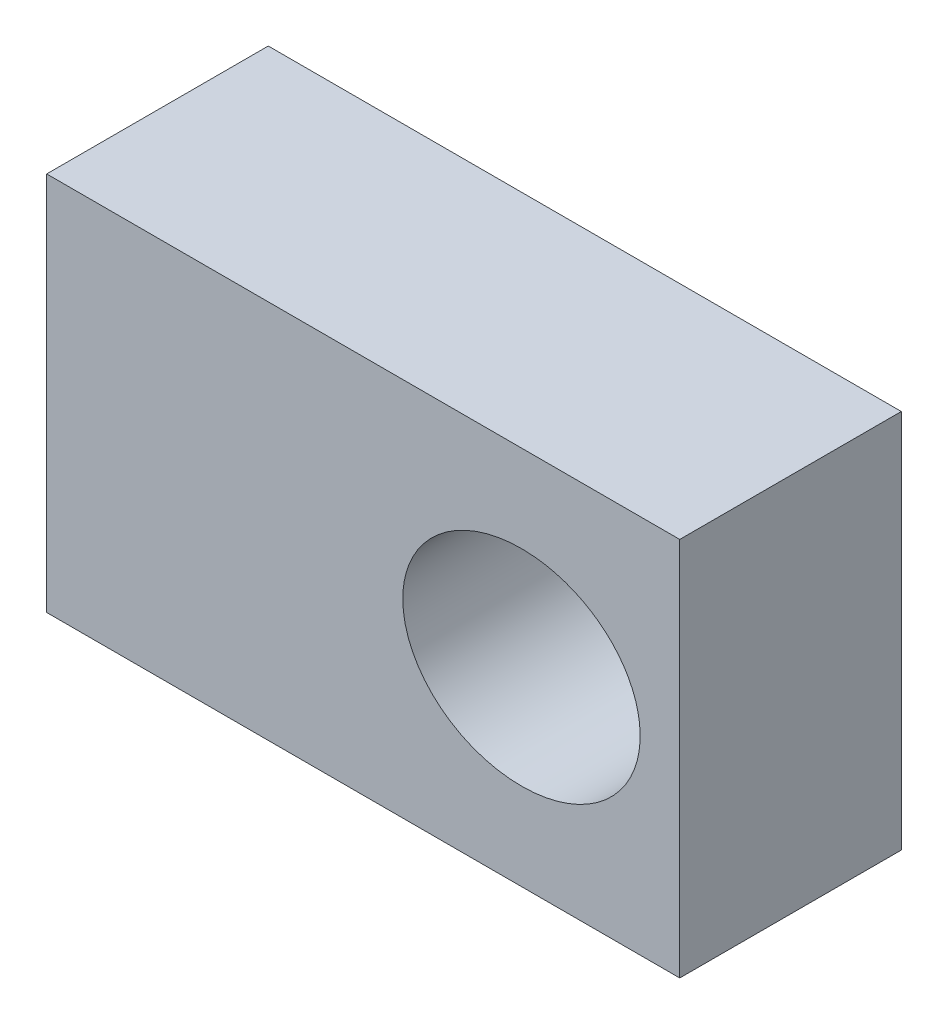
SolidWorks part; units mm, degrees
ref_plane "Front Plane" through (0, 0, 0) normal (0, 0, 1) x (1, 0, 0)
ref_plane "Top Plane" through (0, 0, 0) normal (0, 1, 0) x (1, 0, 0)
ref_plane "Right Plane" through (0, 0, 0) normal (1, 0, 0) x (0, 0, -1)
sketch "Sketch1" plane through (0, 0, 0) normal (0, 0, 1) x (1, 0, 0)
  line L0 (-37.5, 0) -> (37.5, 0) construction
  line L1 (-150, 60) -> (50, 60)
  line L2 (-150, 60) -> (-150, -60)
  line L3 (-150, -60) -> (50, -60)
  line L4 (50, 60) -> (50, -60)
  line L5 (0, 32.5) -> (0, -32.5) construction
  ellipse E0 centre (0, 0) end of major axis (-37.5, 0) minor radius 32.5
  point P17 (50, 0)
  dimension "D1" = 75
  dimension "D2" = 65
  dimension "D3" = 200
  dimension "D4" = 120
  dimension "D5" = 50
extrude "Boss-Extrude1" add sketch "Sketch1" along normal blind 70
sketch "Sketch2" plane through (0, 0, 70) normal (0, 0, 1) x (1, 0, 0)
  ellipse E0 centre (0, 0) end of major axis (-37.5, 0) minor radius 32.5 construction
  point P0 (-37.5, 0)
  point P1 (37.5, 0)
ref_plane "Plane1" through (-37.5, 0, 0) normal (1, 0, 0) x (0, 0, -1)
ref_plane "Plane2" through (37.5, 0, 0) normal (1, 0, 0) x (0, 0, -1)
